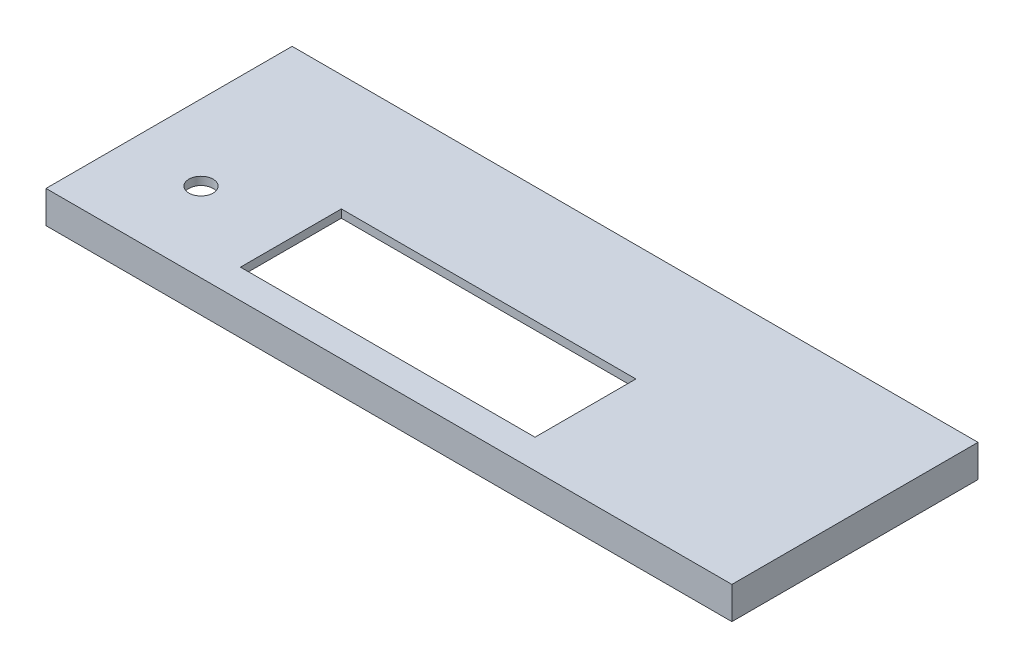
SolidWorks part; units mm, degrees
ref_plane "Front Plane" through (0, 0, 0) normal (0, 0, 1) x (1, 0, 0)
ref_plane "Top Plane" through (0, 0, 0) normal (0, 1, 0) x (1, 0, 0)
ref_plane "Right Plane" through (0, 0, 0) normal (1, 0, 0) x (0, 0, -1)
sketch "Sketch1" plane through (0, 0, 0) normal (0, 1, 0) x (1, 0, 0)
  line L0 (0, 0) -> (88, 0)
  line L2 (0, 0) -> (0, 61)
  line L3 (0, 61) -> (170, 61)
  line L9 (170, 41) -> (170, 61)
  line L10 (88, 0) -> (170, 0)
  line L11 (170, 0) -> (170, 41)
  dimension "D1" = 170
  dimension "D2" = 61
extrude "Boss-Extrude1" add sketch "Sketch1" along normal blind 8
sketch "Sketch9" plane through (0, 0, 0) normal (0, -1, 0) x (1, 0, 0)
  line L0 (0, 0) -> (170, 0) construction
  line L1 (2, -2) -> (168, -2)
  line L2 (2, -2) -> (2, -59)
  line L3 (2, -59) -> (168, -59)
  line L4 (168, -2) -> (168, -59)
  line L5 (0, -61) -> (0, 0) construction
  line L6 (170, -61) -> (0, -61) construction
  line L7 (170, 0) -> (170, -61) construction
  dimension "D1" = 2
  dimension "D2" = 2
  dimension "D3" = 2
  dimension "D4" = 2
extrude "Cut-Extrude5" cut sketch "Sketch9" against normal blind 6
sketch "Sketch10" plane through (0, 0, 0) normal (0, -1, 0) x (1, 0, 0)
  line L0 (168, -2) -> (2, -2) construction
  line L1 (22, -2) -> (32, -2)
  line L2 (22, -2) -> (22, -1)
  line L3 (22, -1) -> (32, -1)
  line L4 (32, -2) -> (32, -1)
  line L5 (2, -59) -> (168, -59) construction
  line L6 (22, -59) -> (32, -59)
  line L7 (22, -59) -> (22, -60)
  line L8 (22, -60) -> (32, -60)
  line L9 (32, -59) -> (32, -60)
  line L10 (170, 0) -> (170, -61) construction
  line L11 (148, -59) -> (138, -59)
  line L12 (148, -59) -> (148, -60)
  line L13 (148, -60) -> (138, -60)
  line L14 (138, -59) -> (138, -60)
  line L15 (148, -2) -> (138, -2)
  line L16 (148, -2) -> (148, -1)
  line L17 (148, -1) -> (138, -1)
  line L18 (138, -2) -> (138, -1)
  line L19 (0, -61) -> (0, 0) construction
  dimension "D1" = 22
  dimension "D2" = 10
  dimension "D3" = 1
  dimension "D4" = 10
  dimension "D5" = 22
  dimension "D6" = 1
  dimension "D7" = 10
  dimension "D8" = 22
  dimension "D9" = 1
  dimension "D10" = 10
  dimension "D11" = 1
  dimension "D12" = 22
extrude "Cut-Extrude6" cut sketch "Sketch10" against normal blind 6
sketch "Sketch11" plane through (22, 0, 0) normal (1, 0, 0) x (0, 0, -1)
  line L0 (2, 6) -> (1, 5)
  line L2 (1, 6) -> (1, 0) construction
  line L9 (2, 6) -> (1, 6) construction
  line L10 (1, 5) -> (1, 4.5)
  line L11 (1, 4.5) -> (1.3536, 4.1464)
  line L12 (1.3536, 4.1464) -> (1.3536, 3.6464)
  line L13 (1.3536, 3.6464) -> (1, 3.2929)
  line L14 (1, 3.2929) -> (1, 4.5)
  line L15 (59, 6) -> (60, 5)
  line L16 (60, 6) -> (60, 0) construction
  line L17 (60, 5) -> (60, 4.5)
  line L18 (60, 6) -> (59, 6) construction
  line L19 (60, 4.5) -> (59.6464, 4.1464)
  line L20 (59.6464, 4.1464) -> (59.6464, 3.6464)
  line L21 (59.6464, 3.6464) -> (60, 3.2929)
  line L22 (60, 3.2929) -> (60, 4.5)
  line M7 (60, 0) -> (60, 6)
  dimension "D1" = 45
  dimension "D2" = 0.5
  dimension "D3" = 0.5
  dimension "D4" = 0.5
  dimension "D5" = 45
  dimension "D6" = 0.5
  dimension "D7" = 0.5
  dimension "D8" = 0.5
extrude "Boss-Extrude4" add sketch "Sketch11" along normal blind 130 contours L14 L13 L12 L11 | L20 L21 L19 M7
sketch "Sketch13" plane through (0, 8, 0) normal (0, 1, 0) x (1, 0, 0)
  line L0 (170, 0) -> (114, 0) construction
  line L1 (0, 0) -> (170, 0) construction
  line L2 (114, 0) -> (114, 7.2) construction
  line L3 (63.2849, 19.7) -> (18.7151, 19.7) construction
  line L4 (114, 7.2) -> (41, 7.2)
  line L5 (114, 7.2) -> (114, 32.2)
  line L6 (114, 32.2) -> (41, 32.2)
  line L7 (41, 7.2) -> (41, 32.2)
  circle A0 centre (18.7151, 19.7) radius 3
  point P12 (41, 19.7)
  dimension "D1" = 56
  dimension "D2" = 7.2
  dimension "D3" = 73
  dimension "D4" = 25
extrude "Cut-Extrude7" cut sketch "Sketch13" against normal blind 130
